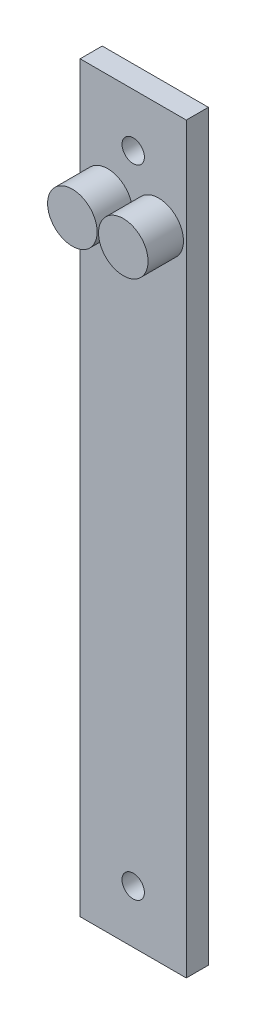
SolidWorks part; units mm, degrees
ref_plane "Front Plane" through (0, 0, 0) normal (0, 0, 1) x (1, 0, 0)
ref_plane "Top Plane" through (0, 0, 0) normal (0, 1, 0) x (1, 0, 0)
ref_plane "Right Plane" through (0, 0, 0) normal (1, 0, 0) x (0, 0, -1)
sketch "Sketch1" plane through (0, 0, 0) normal (0, 0, 1) x (1, 0, 0)
  line L1 (-19.05, 133.35) -> (19.05, 133.35)
  line L2 (-19.05, 133.35) -> (-19.05, -133.35)
  line L3 (-19.05, -133.35) -> (19.05, -133.35)
  line L4 (19.05, 133.35) -> (19.05, -133.35)
  dimension "D1" = 38.1
  dimension "D2" = 19.05
  dimension "D3" = 266.7
  dimension "D4" = 133.35
extrude "Boss-Extrude1" add sketch "Sketch1" along normal blind 7.9375
hole_wizard "O (0.316) Diameter Hole1" positions "Sketch3" profile "Sketch2" hole size "O" standard "ANSI Inch" end condition through all
sketch "Sketch3" plane through (0, 0, 7.9375) normal (0, 0, 1) x (1, 0, 0)
  point P0 (0, 114.3)
  dimension "D1" = 114.3
sketch "Sketch2" plane through (0, 114.3, 7.9375) normal (1, 0, 0) x (0, -1, 0)
  line L0 (0, 0) -> (0, 7.9375)
  line L1 (0, 7.9375) -> (4.0132, 7.9375)
  line L2 (4.0132, 7.9375) -> (4.0132, 0)
  line L5 (4.0132, 0) -> (0, 0)
  line L11 (0, -6.35) -> (0, 107.95) construction
  dimension "Thru Hole Dia." = 8.0264
  dimension "Thru Hole Depth" = 7.9375
mirror "Mirror1" about plane through (0, 0, 0) normal (0, 1, 0) of "O (0.316) Diameter Hole1"
sketch "Sketch4" plane through (0, 0, 7.9375) normal (0, 0, 1) x (1, 0, 0)
  line L0 (19.05, -133.35) -> (19.05, 133.35) construction
  line L1 (-19.05, 133.35) -> (-19.05, -133.35) construction
  line L2 (19.05, 133.35) -> (-19.05, 133.35) construction
  circle A0 centre (-9.144, 95.25) radius 8.89
  circle A1 centre (9.144, 95.25) radius 8.89
  dimension "D1" = 17.78
  dimension "D2" = 17.78
  dimension "D5" = 38.1
  dimension "D6" = 38.1
  dimension "D3" = 9.906
  dimension "D4" = 9.906
extrude "Boss-Extrude2" add sketch "Sketch4" along normal blind 12.7
equation "\"D2@Sketch1\"=\"D1@Sketch1\"/2"
equation "\"D4@Sketch1\"=\"D3@Sketch1\"/2"
equation "\"D2@Sketch4\"=\"D1@Sketch4\""
equation "\"D4@Sketch4\"=\"D3@Sketch4\""
equation "\"D6@Sketch4\"=\"D5@Sketch4\""
